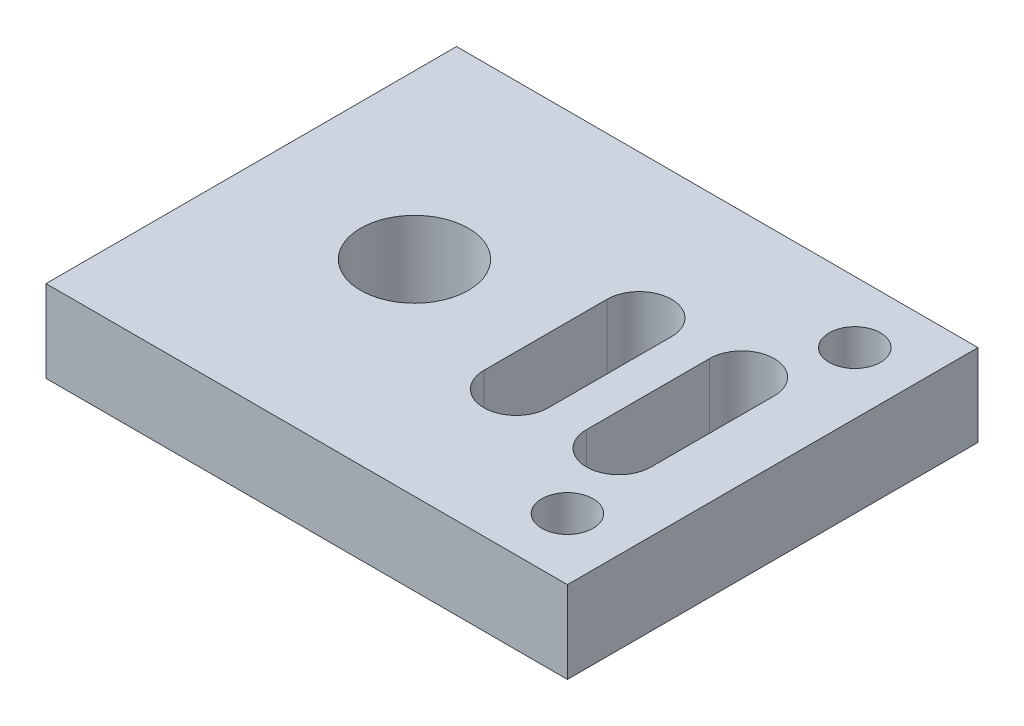
SolidWorks part; units mm, degrees
material "ABS"
ref_plane "Front Plane" through (0, 0, 0) normal (0, 0, 1) x (1, 0, 0)
ref_plane "Top Plane" through (0, 0, 0) normal (0, 1, 0) x (1, 0, 0)
ref_plane "Right Plane" through (0, 0, 0) normal (1, 0, 0) x (0, 0, -1)
sketch "Sketch1" plane through (0, 0, 0) normal (0, 1, 0) x (1, 0, 0)
  line L0 (20.9, 7) -> (20.9, 13) construction
  line L1 (19.325, 7) -> (19.325, 13)
  line L2 (15.9, 7) -> (15.9, 13) construction
  line L3 (14.325, 7) -> (14.325, 13)
  line L4 (25.4, 0) -> (25.4, 20)
  line L5 (25.4, 20) -> (0, 20)
  line L6 (0, 20) -> (0, 0)
  line L7 (0, 0) -> (25.4, 0)
  line L8 (0, 10) -> (25.4, 10) construction
  line L9 (17.475, 7) -> (17.475, 13)
  line L10 (22.475, 7) -> (22.475, 13)
  circle A0 centre (22.4, 17) radius 1.25
  arc A1 (19.325, 7) -> (22.475, 7) centre (20.9, 7) ccw
  arc A2 (22.475, 13) -> (19.325, 13) centre (20.9, 13) ccw
  circle A3 centre (7.95, 10) radius 2.625
  arc A4 (14.325, 7) -> (17.475, 7) centre (15.9, 7) ccw
  arc A5 (17.475, 13) -> (14.325, 13) centre (15.9, 13) ccw
  circle A6 centre (22.4, 3) radius 1.25
  point P4 (20.9, 10)
  point P12 (15.9, 10)
  dimension "D3" = 2.5
  dimension "D4" = 5.25
  dimension "D7" = 1.5
  dimension "D9" = 1.575
  dimension "D1" = 25.4
  dimension "D2" = 20
  dimension "D5" = 14
  dimension "D6" = 3
  dimension "D8" = 5
  dimension "D10" = 6
  dimension "D11" = 7.95
  dimension "D12" = 7.95
extrude "Boss-Extrude1" add sketch "Sketch1" against normal blind 4
